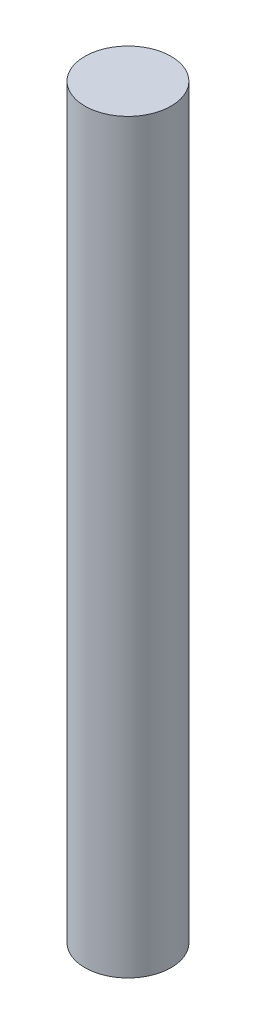
SolidWorks part; units mm, degrees
ref_plane "Front Plane" through (0, 0, 0) normal (0, 0, 1) x (1, 0, 0)
ref_plane "Top Plane" through (0, 0, 0) normal (0, 1, 0) x (1, 0, 0)
ref_plane "Right Plane" through (0, 0, 0) normal (1, 0, 0) x (0, 0, -1)
sketch "Sketch1" plane through (0, 0, 0) normal (0, 1, 0) x (1, 0, 0)
  circle A0 centre (0, 0) radius 3.302
  dimension "D1" = 6.604
extrude "Extrude1" add sketch "Sketch1" along normal blind 57.15
